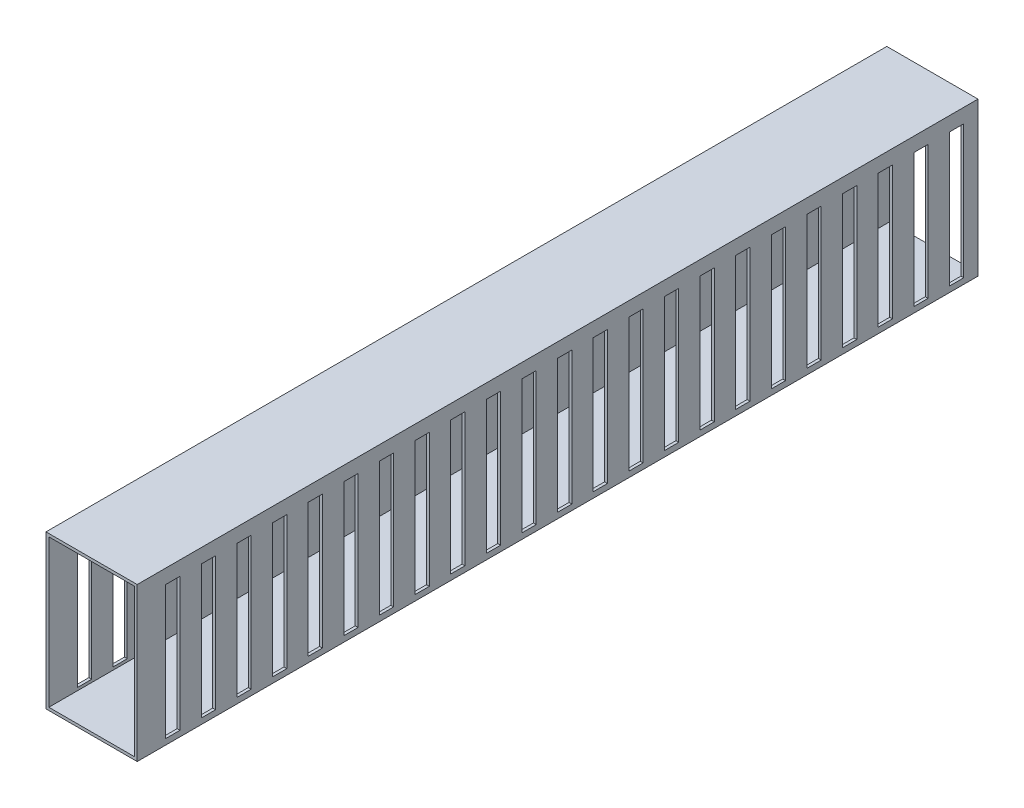
SolidWorks part; units mm, degrees
ref_plane "Plan de face" through (0, 0, 0) normal (0, 0, 1) x (1, 0, 0)
ref_plane "Plan de dessus" through (0, 0, 0) normal (0, 1, 0) x (1, 0, 0)
ref_plane "Plan de droite" through (0, 0, 0) normal (1, 0, 0) x (0, 0, -1)
sketch "Esquisse1" plane through (0, 0, 0) normal (0, 0, 1) x (1, 0, 0)
  line L0 (-12.0229, 36.1361) -> (-12.0229, -15.6639)
  line L1 (-13.0229, 37.1361) -> (18.9771, 37.1361)
  line L2 (-13.0229, 37.1361) -> (-13.0229, -16.6639)
  line L3 (-13.0229, -16.6639) -> (18.9771, -16.6639)
  line L4 (18.9771, 37.1361) -> (18.9771, -16.6639)
  line L5 (-12.0229, -15.6639) -> (17.9771, -15.6639)
  line L6 (17.9771, 36.1361) -> (17.9771, -15.6639)
  line L7 (-12.0229, 36.1361) -> (17.9771, 36.1361)
  dimension "D1" = 32
  dimension "D2" = 53.8
  dimension "D3" = 1
extrude "Boss.-Extru.1" add sketch "Esquisse1" along normal blind 295
sketch "Esquisse2" plane through (18.9771, 0, 0) normal (1, 0, 0) x (0, 0, -1)
  line L0 (-295, -16.6639) -> (0, -16.6639) construction
  line L1 (-5, -14.6639) -> (-10, -14.6639)
  line L2 (-5, -14.6639) -> (-5, 32.1361)
  line L3 (-5, 32.1361) -> (-10, 32.1361)
  line L4 (-10, -14.6639) -> (-10, 32.1361)
  line L5 (0, -16.6639) -> (0, 37.1361) construction
  line L6 (-295, 37.1361) -> (0, 37.1361) construction
  dimension "D1" = 2
  dimension "D2" = 5
  dimension "D3" = 5
  dimension "D4" = 5
extrude "Enlèv. mat.-Extru.1" cut sketch "Esquisse2" against normal up to surface (32 mm away) up to face at (-13.0229, 10.2361, 147.5)
pattern_linear "Répétition linéaire1" count 23 spacing 12.5 along (0, 0, 1) of "Enlèv. mat.-Extru.1"
